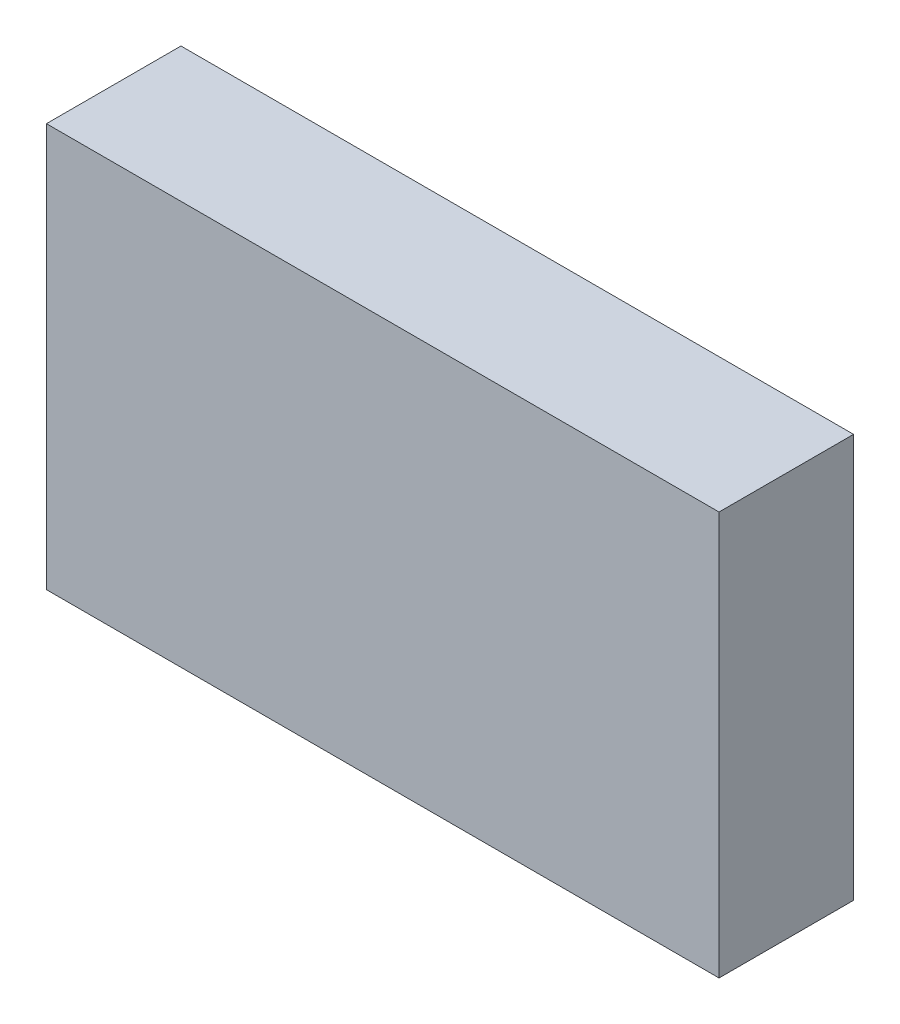
SolidWorks part; units mm, degrees
ref_plane "Front Plane" through (0, 0, 0) normal (0, 0, 1) x (1, 0, 0)
ref_plane "Top Plane" through (0, 0, 0) normal (0, 1, 0) x (1, 0, 0)
ref_plane "Right Plane" through (0, 0, 0) normal (1, 0, 0) x (0, 0, -1)
sketch "Sketch1" plane through (0, 0, 0) normal (0, 0, 1) x (1, 0, 0)
  line L1 (0, 0) -> (10, 0)
  line L2 (0, 0) -> (0, 6)
  line L3 (0, 6) -> (10, 6)
  line L4 (10, 0) -> (10, 6)
  dimension "D1" = 10
  dimension "D2" = 6
extrude "main_body" add sketch "Sketch1" along normal blind 2
sketch "Sketch2" plane through (0, 0, 0) normal (0, 0, -1) x (-1, 0, 0)
  line L0 (0, 0) -> (-10, 0) construction
  line L1 (-10, 0) -> (-10, 6) construction
  circle A0 centre (-5, 3) radius 2.5
  dimension "D1" = 5
  dimension "D2" = 3
  dimension "D3" = 5
extrude "shaft_cut" cut sketch "Sketch2" against normal blind 1
